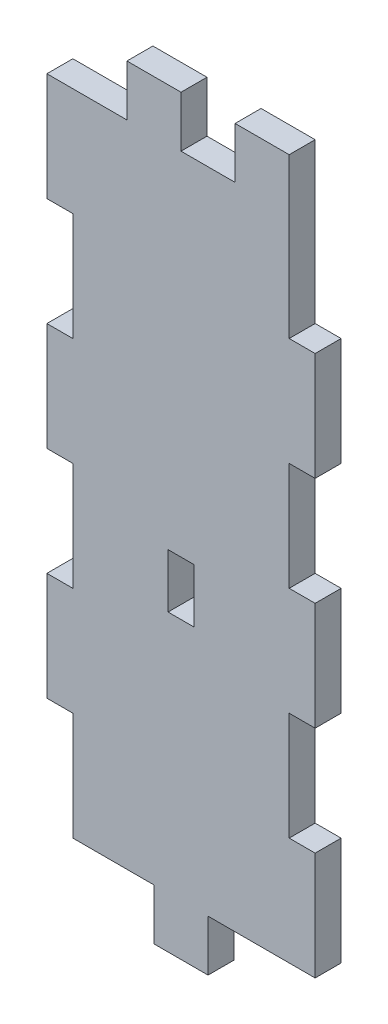
SolidWorks part; units mm, degrees
material "Acrylic (Medium-high impact)"
ref_plane "Front Plane" through (0, 0, 0) normal (0, 0, 1) x (1, 0, 0)
ref_plane "Top Plane" through (0, 0, 0) normal (0, 1, 0) x (1, 0, 0)
ref_plane "Right Plane" through (0, 0, 0) normal (1, 0, 0) x (0, 0, -1)
sketch "Sketch1" plane through (0, 0, 0) normal (0, 0, 1) x (1, 0, 0)
  line L0 (0, 0) -> (0, 12.7)
  line L1 (0, 12.7) -> (-3.048, 12.7)
  line L2 (-3.048, 12.7) -> (-3.048, 25.4)
  line L3 (-3.048, 25.4) -> (0, 25.4)
  line L4 (0, 25.4) -> (0, 38.1)
  line L5 (0, 38.1) -> (-3.048, 38.1)
  line L6 (-3.048, 38.1) -> (-3.048, 50.8)
  line L7 (-3.048, 50.8) -> (0, 50.8)
  line L8 (0, 50.8) -> (0, 63.5)
  line L9 (0, 63.5) -> (-3.048, 63.5)
  line L10 (-3.048, 63.5) -> (-3.048, 76.2)
  line L11 (-3.048, 76.2) -> (6.35, 76.2)
  line L12 (6.35, 76.2) -> (6.35, 82.1944)
  line L13 (6.35, 82.1944) -> (12.7, 82.1944)
  line L14 (12.7, 82.1944) -> (12.7, 76.2)
  line L15 (12.7, 76.2) -> (19.05, 76.2)
  line L16 (19.05, 76.2) -> (19.05, 82.1944)
  line L17 (19.05, 82.1944) -> (25.4, 82.1944)
  line L18 (25.4, 82.1944) -> (25.4, 63.5)
  line L19 (25.4, 63.5) -> (28.448, 63.5)
  line L20 (28.448, 63.5) -> (28.448, 50.8)
  line L21 (28.448, 50.8) -> (25.4, 50.8)
  line L22 (25.4, 50.8) -> (25.4, 38.1)
  line L23 (25.4, 38.1) -> (28.448, 38.1)
  line L24 (28.448, 38.1) -> (28.448, 25.4)
  line L25 (28.448, 25.4) -> (25.4, 25.4)
  line L26 (25.4, 25.4) -> (25.4, 12.7)
  line L27 (25.4, 12.7) -> (28.448, 12.7)
  line L28 (28.448, 12.7) -> (28.448, 0)
  line L29 (28.448, 0) -> (15.875, 0)
  line L30 (15.875, 0) -> (15.875, -5.9944)
  line L31 (15.875, -5.9944) -> (9.525, -5.9944)
  line L32 (9.525, -5.9944) -> (9.525, 0)
  line L33 (9.525, 0) -> (0, 0)
  line L35 (14.224, 34.925) -> (11.176, 34.925)
  line L36 (14.224, 34.925) -> (14.224, 28.575)
  line L37 (14.224, 28.575) -> (11.176, 28.575)
  line L38 (11.176, 34.925) -> (11.176, 28.575)
  point P39 (12.7, 28.575)
  point P40 (12.7, -5.9944)
  dimension "D1" = 12.7
  dimension "D2" = 3.048
  dimension "D3" = 6.35
  dimension "D4" = 5.9944
  dimension "D6" = 9.398
  dimension "D7" = 6.35
  dimension "D8" = 5.9944
  dimension "D9" = 9.525
  dimension "D10" = 76.2
  dimension "D11" = 3.048
  dimension "D12" = 6.35
  dimension "D13" = 34.925
extrude "Boss-Extrude1" add sketch "Sketch1" along normal blind 3.048
